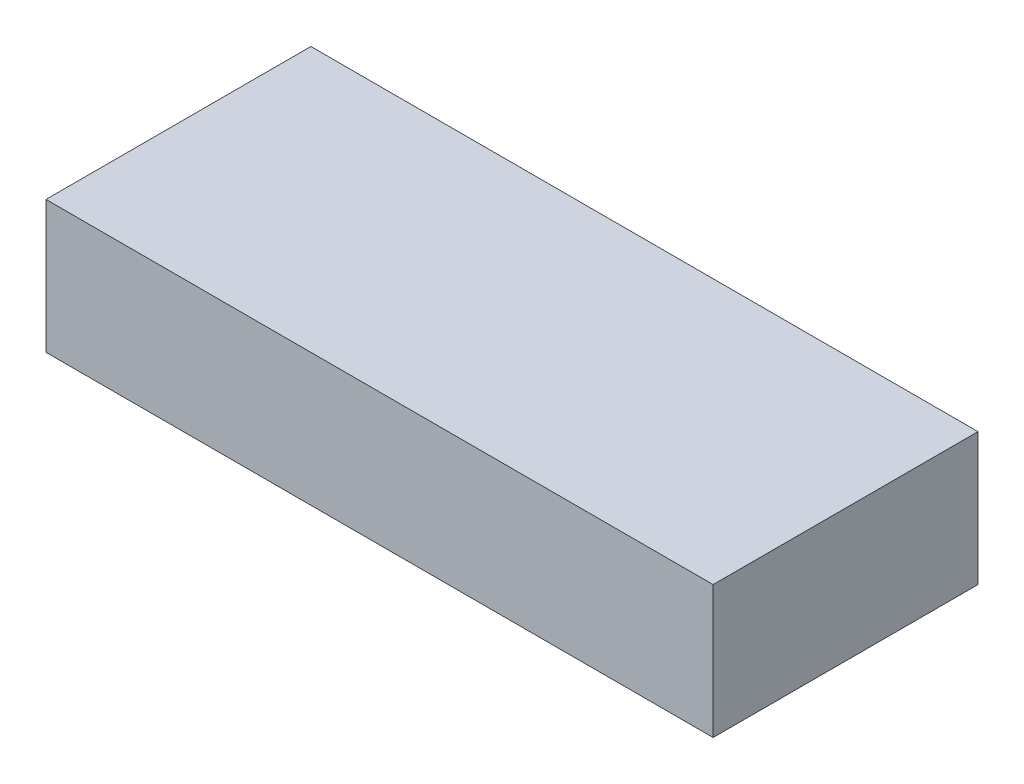
SolidWorks part; units mm, degrees
material "6061 Alloy"
ref_plane "Front Plane" through (0, 0, 0) normal (0, 0, 1) x (1, 0, 0)
ref_plane "Top Plane" through (0, 0, 0) normal (0, 1, 0) x (1, 0, 0)
ref_plane "Right Plane" through (0, 0, 0) normal (1, 0, 0) x (0, 0, -1)
sketch "Sketch1" plane through (0, 0, 0) normal (0, 1, 0) x (1, 0, 0)
  line L1 (-215.9, -85.725) -> (215.9, -85.725)
  line L2 (-215.9, -85.725) -> (-215.9, 85.725)
  line L3 (-215.9, 85.725) -> (215.9, 85.725)
  line L4 (215.9, -85.725) -> (215.9, 85.725)
  line L5 (-215.9, -85.725) -> (215.9, 85.725) construction
  line L6 (-215.9, 85.725) -> (215.9, -85.725) construction
  point P0 (0, 0)
  dimension "D1" = 431.8
  dimension "D2" = 171.45
extrude "Boss-Extrude1" add sketch "Sketch1" along normal blind 85.725
sketch "Sketch2" plane through (0, 0, 0) normal (0, -1, 0) x (1, 0, 0)
  line L0 (-178.8064, -72.1404) -> (-178.8064, -85.725) construction
  line L1 (215.9, -85.725) -> (-215.9, -85.725) construction
  line L2 (-202.3154, -48.6314) -> (-215.9, -48.6314) construction
  line L3 (-215.9, -85.725) -> (-215.9, 85.725) construction
  line L4 (178.8064, -72.1404) -> (178.8064, -85.725) construction
  line L5 (202.3154, -48.6314) -> (215.9, -48.6314) construction
  line L6 (215.9, 85.725) -> (215.9, -85.725) construction
  line L7 (-178.8064, 72.1404) -> (-178.8064, 85.725) construction
  line L8 (-215.9, 85.725) -> (215.9, 85.725) construction
  line L9 (-202.3154, 48.6314) -> (-215.9, 48.6314) construction
  line L10 (202.3154, 48.6314) -> (215.9, 48.6314) construction
  line L11 (178.8064, 72.1404) -> (178.8064, 85.725)
  line L18 (178.8064, 72.1404) -> (-178.8064, 72.1404)
  line L19 (202.3154, -48.6314) -> (202.3154, 48.6314)
  line L20 (-178.8064, -72.1404) -> (178.8064, -72.1404)
  line L21 (-202.3154, 48.6314) -> (-202.3154, -48.6314)
  arc A0 (202.3154, -48.6314) -> (178.8064, -72.1404) centre (178.8064, -48.6314) cw
  arc A1 (178.8064, 72.1404) -> (202.3154, 48.6314) centre (178.8064, 48.6314) cw
  arc A2 (-178.8064, 72.1404) -> (-202.3154, 48.6314) centre (-178.8064, 48.6314) ccw
  arc A3 (-178.8064, -72.1404) -> (-202.3154, -48.6314) centre (-178.8064, -48.6314) cw
  dimension "D2" = 23.509
extrude "Cut-Extrude1" cut sketch "Sketch2" against normal offset from surface (73.025 mm away) 12.7 contours A1 L19 A0 L20 A3 L21 A2 L18 up to face at (0, 85.725, 0)
sketch "Sketch4" plane through (0, 73.025, 0) normal (0, -1, 0) x (1, 0, 0)
  line L0 (-202.3154, -6.35) -> (-202.3154, 6.35)
  line L2 (-202.3154, 48.6314) -> (-202.3154, -48.6314) construction
  line L3 (-202.3154, 6.35) -> (-75.9051, 6.35)
  line L4 (-75.9051, 6.35) -> (-75.9051, 72.1404)
  line L5 (-178.8064, 72.1404) -> (178.8064, 72.1404) construction
  line L6 (-75.9051, 72.1404) -> (-63.2051, 72.1404)
  line L7 (-63.2051, 72.1404) -> (-63.2051, 6.35)
  line L8 (-63.2051, 6.35) -> (63.2051, 6.35)
  line L9 (63.2051, 6.35) -> (63.2051, 72.1404)
  line L10 (63.2051, 72.1404) -> (75.9051, 72.1404)
  line L11 (75.9051, 72.1404) -> (75.9051, 6.35)
  line L12 (75.9051, 6.35) -> (202.3154, 6.35)
  line L13 (202.3154, 48.6314) -> (202.3154, -48.6314) construction
  line L14 (202.3154, 6.35) -> (202.3154, -6.35)
  line L15 (202.3154, -6.35) -> (75.9051, -6.35)
  line L16 (75.9051, -6.35) -> (75.9051, -72.1404)
  line L17 (178.8064, -72.1404) -> (-178.8064, -72.1404) construction
  line L18 (75.9051, -72.1404) -> (63.2051, -72.1404)
  line L19 (-178.8064, -72.1404) -> (178.8064, -72.1404) construction
  line L20 (63.2051, -72.1404) -> (63.2051, -6.35)
  line L21 (63.2051, -6.35) -> (-63.2051, -6.35)
  line L22 (-63.2051, -6.35) -> (-63.2051, -72.1404)
  line L23 (-63.2051, -72.1404) -> (-75.9051, -72.1404)
  line L24 (-75.9051, -72.1404) -> (-75.9051, -6.35)
  line L25 (-75.9051, -6.35) -> (-202.3154, -6.35)
  point P3 (-202.3154, 0)
  dimension "D1" = 12.7
extrude "Boss-Extrude3" [suppressed] add sketch "Sketch4" along normal blind 6.35
fillet "Fillet1" [suppressed] radius 19.05
chamfer "Chamfer1" distance 0.635 8 edges at (195.4298, 0, -65.2548) (202.3154, 0, 0) (195.4298, 0, 65.2548) (0, 0, 72.1404) (-195.4298, 0, 65.2548) (0, 0, -72.1404) (-202.3154, 0, 0) (-195.4298, 0, -65.2548)
sketch "Sketch7" plane through (0, 0, 0) normal (0, -1, 0) x (1, 0, 0)
  line L0 (-215.9, -85.725) -> (-215.9, 85.725) construction
  line L1 (215.9, -85.725) -> (-215.9, -85.725) construction
  line L2 (215.9, 85.725) -> (215.9, -85.725) construction
  line L3 (-215.9, 85.725) -> (215.9, 85.725) construction
  line L4 (-215.9, -85.725) -> (-215.9, 85.725)
  line L5 (215.9, -85.725) -> (-215.9, -85.725)
  line L6 (215.9, 85.725) -> (215.9, -85.725)
  line L7 (-215.9, 85.725) -> (215.9, 85.725)
  line L36 (-171.45, -85.725) -> (26.4895, -85.725)
  line L37 (30.9796, -87.5849) -> (46.3099, -102.9151)
  line L38 (50.8, -104.775) -> (95.25, -104.775)
  line L39 (99.7401, -102.9151) -> (115.0704, -87.5849)
  line L40 (119.5605, -85.725) -> (190.5, -85.725)
  line L41 (194.9901, -87.5849) -> (210.3204, -102.9151)
  line L42 (214.8105, -104.775) -> (228.6, -104.775)
  line L43 (234.95, -98.425) -> (234.95, -53.975)
  line L44 (228.6, -47.625) -> (222.25, -47.625)
  line L45 (215.9, -41.275) -> (215.9, 41.275)
  line L46 (222.25, 47.625) -> (228.6, 47.625)
  line L47 (234.95, 53.975) -> (234.95, 98.425)
  line L48 (228.6, 104.775) -> (214.8105, 104.775)
  line L49 (210.3204, 102.9151) -> (194.9901, 87.5849)
  line L50 (190.5, 85.725) -> (119.5605, 85.725)
  line L51 (115.0704, 87.5849) -> (99.7401, 102.9151)
  line L52 (95.25, 104.775) -> (50.8, 104.775)
  line L53 (46.3099, 102.9151) -> (30.9796, 87.5849)
  line L54 (26.4895, 85.725) -> (-171.45, 85.725)
  line L55 (-177.8, 92.075) -> (-177.8, 98.425)
  line L56 (-184.15, 104.775) -> (-228.6, 104.775)
  line L57 (-234.95, 98.425) -> (-234.95, 53.975)
  line L58 (-228.6, 47.625) -> (-222.25, 47.625)
  line L59 (-215.9, 41.275) -> (-215.9, -41.275)
  line L60 (-222.25, -47.625) -> (-228.6, -47.625)
  line L61 (-234.95, -53.975) -> (-234.95, -98.425)
  line L62 (-228.6, -104.775) -> (-184.15, -104.775)
  line L63 (-177.8, -98.425) -> (-177.8, -92.075)
  line L64 (-171.45, -85.725) -> (26.4895, -85.725)
  line L65 (30.9796, -87.5849) -> (46.3099, -102.9151)
  line L66 (50.8, -104.775) -> (95.25, -104.775)
  line L67 (99.7401, -102.9151) -> (115.0704, -87.5849)
  line L68 (119.5605, -85.725) -> (190.5, -85.725)
  line L69 (194.9901, -87.5849) -> (210.3204, -102.9151)
  line L70 (214.8105, -104.775) -> (228.6, -104.775)
  line L71 (234.95, -98.425) -> (234.95, -53.975)
  line L72 (228.6, -47.625) -> (222.25, -47.625)
  line L73 (215.9, -41.275) -> (215.9, 41.275)
  line L74 (222.25, 47.625) -> (228.6, 47.625)
  line L75 (234.95, 53.975) -> (234.95, 98.425)
  line L76 (228.6, 104.775) -> (214.8105, 104.775)
  line L77 (210.3204, 102.9151) -> (194.9901, 87.5849)
  line L78 (190.5, 85.725) -> (119.5605, 85.725)
  line L79 (115.0704, 87.5849) -> (99.7401, 102.9151)
  line L80 (95.25, 104.775) -> (50.8, 104.775)
  line L81 (46.3099, 102.9151) -> (30.9796, 87.5849)
  line L82 (26.4895, 85.725) -> (-171.45, 85.725)
  line L83 (-177.8, 92.075) -> (-177.8, 98.425)
  line L84 (-184.15, 104.775) -> (-228.6, 104.775)
  line L85 (-234.95, 98.425) -> (-234.95, 53.975)
  line L86 (-228.6, 47.625) -> (-222.25, 47.625)
  line L87 (-215.9, 41.275) -> (-215.9, -41.275)
  line L88 (-222.25, -47.625) -> (-228.6, -47.625)
  line L89 (-234.95, -53.975) -> (-234.95, -98.425)
  line L90 (-228.6, -104.775) -> (-184.15, -104.775)
  line L91 (-177.8, -98.425) -> (-177.8, -92.075)
  circle A0 centre (53.975, 95.25) radius 3.2639 construction
  circle A1 centre (92.075, 95.25) radius 3.2639 construction
  circle A2 centre (225.425, 95.25) radius 3.2639 construction
  circle A3 centre (225.425, 57.15) radius 3.2639 construction
  circle A4 centre (225.425, -57.15) radius 3.2639 construction
  circle A5 centre (225.425, -95.25) radius 3.2639 construction
  circle A6 centre (92.075, -95.25) radius 3.2639 construction
  circle A7 centre (53.975, -95.25) radius 3.2639 construction
  circle A8 centre (-187.325, -95.25) radius 3.2639 construction
  circle A9 centre (-225.425, -95.25) radius 3.2639 construction
  circle A10 centre (-225.425, -57.15) radius 3.2639 construction
  circle A11 centre (-225.425, 57.15) radius 3.2639 construction
  circle A12 centre (-187.325, 95.25) radius 3.2639 construction
  circle A13 centre (-225.425, 95.25) radius 3.2639 construction
  circle A14 centre (53.975, 95.25) radius 3.2639
  circle A15 centre (92.075, 95.25) radius 3.2639
  circle A16 centre (225.425, 95.25) radius 3.2639
  circle A17 centre (225.425, 57.15) radius 3.2639
  circle A18 centre (225.425, -57.15) radius 3.2639
  circle A19 centre (225.425, -95.25) radius 3.2639
  circle A20 centre (92.075, -95.25) radius 3.2639
  circle A21 centre (53.975, -95.25) radius 3.2639
  circle A22 centre (-187.325, -95.25) radius 3.2639
  circle A23 centre (-225.425, -95.25) radius 3.2639
  circle A24 centre (-225.425, -57.15) radius 3.2639
  circle A25 centre (-225.425, 57.15) radius 3.2639
  circle A26 centre (-187.325, 95.25) radius 3.2639
  circle A27 centre (-225.425, 95.25) radius 3.2639
  arc A28 (-171.45, -85.725) -> (-177.8, -92.075) centre (-171.45, -92.075) ccw
  arc A29 (30.9796, -87.5849) -> (26.4895, -85.725) centre (26.4895, -92.075) ccw
  arc A30 (46.3099, -102.9151) -> (50.8, -104.775) centre (50.8, -98.425) ccw
  arc A31 (95.25, -104.775) -> (99.7401, -102.9151) centre (95.25, -98.425) ccw
  arc A32 (119.5605, -85.725) -> (115.0704, -87.5849) centre (119.5605, -92.075) ccw
  arc A33 (194.9901, -87.5849) -> (190.5, -85.725) centre (190.5, -92.075) ccw
  arc A34 (210.3204, -102.9151) -> (214.8105, -104.775) centre (214.8105, -98.425) ccw
  arc A35 (228.6, -104.775) -> (234.95, -98.425) centre (228.6, -98.425) ccw
  arc A36 (234.95, -53.975) -> (228.6, -47.625) centre (228.6, -53.975) ccw
  arc A37 (215.9, -41.275) -> (222.25, -47.625) centre (222.25, -41.275) ccw
  arc A38 (222.25, 47.625) -> (215.9, 41.275) centre (222.25, 41.275) ccw
  arc A39 (228.6, 47.625) -> (234.95, 53.975) centre (228.6, 53.975) ccw
  arc A40 (234.95, 98.425) -> (228.6, 104.775) centre (228.6, 98.425) ccw
  arc A41 (214.8105, 104.775) -> (210.3204, 102.9151) centre (214.8105, 98.425) ccw
  arc A42 (190.5, 85.725) -> (194.9901, 87.5849) centre (190.5, 92.075) ccw
  arc A43 (115.0704, 87.5849) -> (119.5605, 85.725) centre (119.5605, 92.075) ccw
  arc A44 (99.7401, 102.9151) -> (95.25, 104.775) centre (95.25, 98.425) ccw
  arc A45 (50.8, 104.775) -> (46.3099, 102.9151) centre (50.8, 98.425) ccw
  arc A46 (26.4895, 85.725) -> (30.9796, 87.5849) centre (26.4895, 92.075) ccw
  arc A47 (-177.8, 92.075) -> (-171.45, 85.725) centre (-171.45, 92.075) ccw
  arc A48 (-177.8, 98.425) -> (-184.15, 104.775) centre (-184.15, 98.425) ccw
  arc A49 (-228.6, 104.775) -> (-234.95, 98.425) centre (-228.6, 98.425) ccw
  arc A50 (-234.95, 53.975) -> (-228.6, 47.625) centre (-228.6, 53.975) ccw
  arc A51 (-215.9, 41.275) -> (-222.25, 47.625) centre (-222.25, 41.275) ccw
  arc A52 (-222.25, -47.625) -> (-215.9, -41.275) centre (-222.25, -41.275) ccw
  arc A53 (-228.6, -47.625) -> (-234.95, -53.975) centre (-228.6, -53.975) ccw
  arc A54 (-234.95, -98.425) -> (-228.6, -104.775) centre (-228.6, -98.425) ccw
  arc A55 (-184.15, -104.775) -> (-177.8, -98.425) centre (-184.15, -98.425) ccw
  arc A56 (-171.45, -85.725) -> (-177.8, -92.075) centre (-171.45, -92.075) ccw
  arc A57 (30.9796, -87.5849) -> (26.4895, -85.725) centre (26.4895, -92.075) ccw
  arc A58 (46.3099, -102.9151) -> (50.8, -104.775) centre (50.8, -98.425) ccw
  arc A59 (95.25, -104.775) -> (99.7401, -102.9151) centre (95.25, -98.425) ccw
  arc A60 (119.5605, -85.725) -> (115.0704, -87.5849) centre (119.5605, -92.075) ccw
  arc A61 (194.9901, -87.5849) -> (190.5, -85.725) centre (190.5, -92.075) ccw
  arc A62 (210.3204, -102.9151) -> (214.8105, -104.775) centre (214.8105, -98.425) ccw
  arc A63 (228.6, -104.775) -> (234.95, -98.425) centre (228.6, -98.425) ccw
  arc A64 (234.95, -53.975) -> (228.6, -47.625) centre (228.6, -53.975) ccw
  arc A65 (215.9, -41.275) -> (222.25, -47.625) centre (222.25, -41.275) ccw
  arc A66 (222.25, 47.625) -> (215.9, 41.275) centre (222.25, 41.275) ccw
  arc A67 (228.6, 47.625) -> (234.95, 53.975) centre (228.6, 53.975) ccw
  arc A68 (234.95, 98.425) -> (228.6, 104.775) centre (228.6, 98.425) ccw
  arc A69 (214.8105, 104.775) -> (210.3204, 102.9151) centre (214.8105, 98.425) ccw
  arc A70 (190.5, 85.725) -> (194.9901, 87.5849) centre (190.5, 92.075) ccw
  arc A71 (115.0704, 87.5849) -> (119.5605, 85.725) centre (119.5605, 92.075) ccw
  arc A72 (99.7401, 102.9151) -> (95.25, 104.775) centre (95.25, 98.425) ccw
  arc A73 (50.8, 104.775) -> (46.3099, 102.9151) centre (50.8, 98.425) ccw
  arc A74 (26.4895, 85.725) -> (30.9796, 87.5849) centre (26.4895, 92.075) ccw
  arc A75 (-177.8, 92.075) -> (-171.45, 85.725) centre (-171.45, 92.075) ccw
  arc A76 (-177.8, 98.425) -> (-184.15, 104.775) centre (-184.15, 98.425) ccw
  arc A77 (-228.6, 104.775) -> (-234.95, 98.425) centre (-228.6, 98.425) ccw
  arc A78 (-234.95, 53.975) -> (-228.6, 47.625) centre (-228.6, 53.975) ccw
  arc A79 (-215.9, 41.275) -> (-222.25, 47.625) centre (-222.25, 41.275) ccw
  arc A80 (-222.25, -47.625) -> (-215.9, -41.275) centre (-222.25, -41.275) ccw
  arc A81 (-228.6, -47.625) -> (-234.95, -53.975) centre (-228.6, -53.975) ccw
  arc A82 (-234.95, -98.425) -> (-228.6, -104.775) centre (-228.6, -98.425) ccw
  arc A83 (-184.15, -104.775) -> (-177.8, -98.425) centre (-184.15, -98.425) ccw
  line M69 (215.9, -85.725) -> (215.9, 85.725)
  line M70 (215.9, 85.725) -> (-215.9, 85.725)
  line M71 (-215.9, 85.725) -> (-215.9, -85.725)
  line M72 (-215.9, -85.725) -> (215.9, -85.725)
  dimension "D1" = 0
extrude "Boss-Extrude4" [suppressed] add sketch "Sketch7" against normal blind 6.35 contours A79 A75 L83 A76 L84 A77 L85 A78 L86 A27 A26 A25 M71 M70 | A74 A71 L79 A72 L80 A73 L81 A14 A15 M70 | A70 A66 L74 A67 L75 A68 L76 A69 L77 A17 A16 M70 M69 | A65 A61 L69 A62 L70 A63 L71 A64 L72 A18 A19 M69 M72 | A60 A57 L65 A58 L66 A59 L67 A21 A20 M72 | L90 A83 L91 A56 A80 L88 A81 L89 A82 A24 A23 A22 M72 M71
equation "\"oring.277.ID\"= 11.484in"
equation "\"oring.277.A\"= 11.750in"
equation "\"oring.277.A1\"= 11.722in"
equation "\"oring.277.B\"= 11.500in"
equation "\"oring.277.B1\"= 11.528in"
equation "\"oring.277.C\"= 11.747in"
equation "\"oring.277.D\"= 11.503in"
equation "\"oring.277.G\"= 0.187in"
equation "\"D1@Sketch2\" = ( \"oring.279.A\" + \"anodize.add\" * 2 ) * PI"
equation "\"D2@Sketch2\"= 6 * \"oring.279.W\" + ( \"oring.279.C.factor\" - \"oring.279.B1\" ) / 2"
equation "\"oring.277.W\"= 0.139in"
equation "\"anodize.add\"= 0.001in"
equation "\"c.factor\"= 0.00271"
equation "\"oring.277.C.factor\"= \"oring.277.C\" - \"oring.277.C\" * \"c.factor\""
equation "\"oring.279.ID\"= 12.984in"
equation "\"oring.279.A\"= 13.250in"
equation "\"oring.279.A1\"= 13.222in"
equation "\"oring.279.B\"= 13.000in"
equation "\"oring.279.B1\"= 13.028in"
equation "\"oring.279.C\"= 13.247in"
equation "\"oring.279.D\"= 13.003in"
equation "\"oring.279.G\"= 0.187in"
equation "\"oring.279.W\"= 0.139in"
equation "\"oring.279.C.factor\"= \"oring.279.C\" - \"oring.279.C\" * \"c.factor\""
